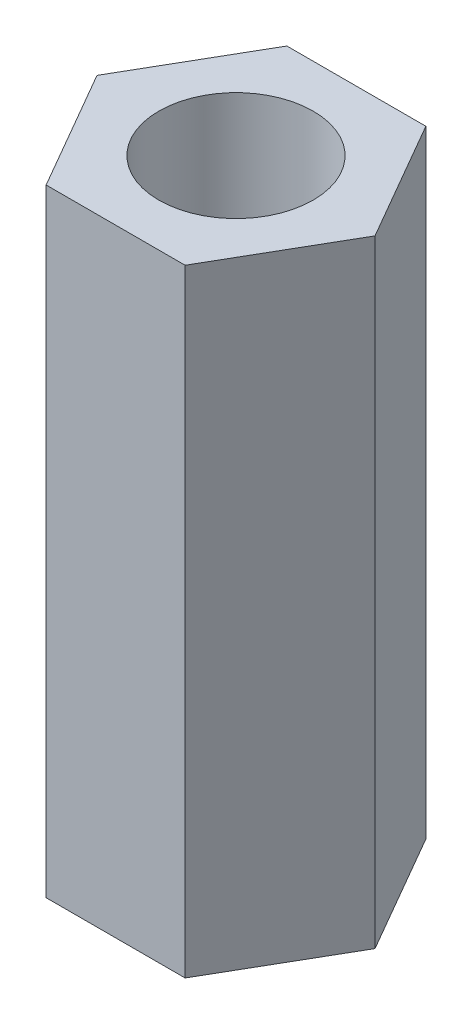
SolidWorks part; units mm, degrees
material "黄铜"
ref_plane "前视基准面" through (0, 0, 0) normal (0, 0, 1) x (1, 0, 0)
ref_plane "上视基准面" through (0, 0, 0) normal (0, 1, 0) x (1, 0, 0)
ref_plane "右视基准面" through (0, 0, 0) normal (1, 0, 0) x (0, 0, -1)
sketch "草图1" plane through (0, 0, 0) normal (0, 1, 0) x (1, 0, 0)
  line L1 (2.2517, 0) -> (1.1258, 1.95)
  line L2 (1.1258, 1.95) -> (-1.1258, 1.95)
  line L3 (-1.1258, 1.95) -> (-2.2517, 0)
  line L4 (-2.2517, 0) -> (-1.1258, -1.95)
  line L5 (-1.1258, -1.95) -> (1.1258, -1.95)
  line L6 (1.1258, -1.95) -> (2.2517, 0)
  circle A0 centre (0, 0) radius 1.95 construction
  dimension "D1" = 3.9
extrude "凸台-拉伸1" add sketch "草图1" along normal blind 10
sketch "草图2" plane through (0, 10, 0) normal (0, 1, 0) x (1, 0, 0)
  circle A0 centre (0, 0) radius 1.25
  dimension "D1" = 2.5
extrude "切除-拉伸1" cut sketch "草图2" against normal through all
